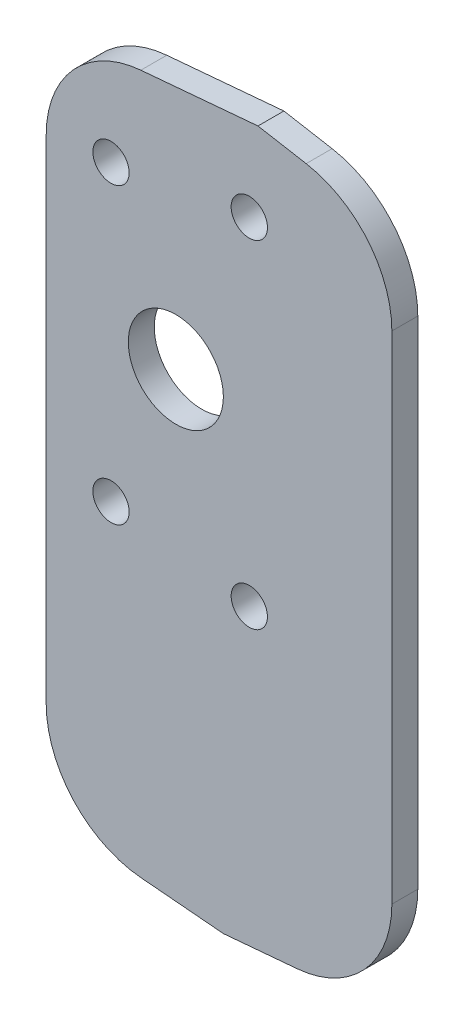
SolidWorks part; units mm, degrees
ref_plane "Face" through (0, 0, 0) normal (0, 0, 1) x (1, 0, 0)
ref_plane "Dessus" through (0, 0, 0) normal (0, 1, 0) x (1, 0, 0)
ref_plane "Droite" through (0, 0, 0) normal (1, 0, 0) x (0, 0, -1)
sketch "Esquisse2" plane through (0, 0, 0) normal (0, 0, 1) x (1, 0, 0)
  line L0 (-5.9599, 64.5276) -> (18.5449, 66.6715)
  line L1 (18.5449, 66.6715) -> (34.0401, 63.9392)
  line L2 (34.0401, 63.9392) -> (34.0401, -14.5608)
  line L3 (34.0401, -14.5608) -> (14.5449, -16.2664)
  line L4 (14.5449, -16.2664) -> (-5.9599, -14.4724)
  line L5 (-5.9599, -14.4724) -> (-5.9599, 64.5276)
  dimension "D1" = 95
  dimension "D2" = 100
  dimension "D3" = 95
  dimension "D4" = 95
  dimension "D5" = 40
  dimension "D6" = 4
  dimension "D7" = 79
  dimension "D8" = 78.5
extrude "Extrusion1" add sketch "Esquisse2" along normal blind 3
sketch "Esquisse3" plane through (0, 0, 3) normal (0, 0, 1) x (1, 0, 0)
  line L0 (-5.9599, 64.5276) -> (-5.9599, -14.4724) construction
  circle A0 centre (9.0401, 37.5276) radius 5.5
  dimension "D2" = 11
  dimension "D1" = 27
  dimension "D3" = 15
extrude "Enlèv. mat.-Extru.1" cut sketch "Esquisse3" against normal through all
fillet "Congé1" radius 12
sketch "Esquisse7" plane through (0, 0, 3) normal (0, 0, 1) x (1, 0, 0)
  circle A0 centre (9.0401, 37.5276) radius 5.5 construction
  point P0 (1.5401, 54.5276)
  point P1 (17.5401, 57.0276)
  point P2 (1.5401, 20.5276)
  point P3 (17.5401, 18.0276)
  dimension "D1" = 17
  dimension "D2" = 17
  dimension "D6" = 8.5
  dimension "D8" = 7.5
  dimension "D3" = 19.5
  dimension "D4" = 19.5
  dimension "D5" = 7.5
  dimension "D7" = 8.5
hole_wizard "Trou taraudé M5x0.82" positions "Esquisse3D3" profile "Esquisse8" tap size "M5x0.8" standard "ISO"
sketch3d "Esquisse3D3"
  point P0 (1.5401, 54.5276, 3)
  point P2 (17.5401, 57.0276, 3)
  point P4 (1.5401, 20.5276, 3)
  point P6 (17.5401, 18.0276, 3)
sketch "Esquisse8" plane through (1.5401, 54.5276, 3) normal (1, 0, 0) x (0, -1, 0)
  line L0 (0, 0) -> (0, 4.2618)
  line L1 (0, 4.2618) -> (2.1, 3)
  line L2 (2.1, 3) -> (2.1, 0)
  line L5 (2.1, 0) -> (0, 0)
  line L10 (0, 4.2618) -> (-2.1, 3) construction
  line L11 (0, -6.35) -> (0, 107.95) construction
  dimension "Diamètre du trou pour taraudage" = 4.2
  dimension "Profondeur du trou pour taraudage" = 3
  dimension "Angle de pointe" = 118
cosmetic thread "Représentation de filetage6" parameters "D1"=3, "D2"=5
cosmetic thread "Représentation de filetage7" parameters "D1"=3, "D2"=5
cosmetic thread "Représentation de filetage8" parameters "D1"=3, "D2"=5
cosmetic thread "Représentation de filetage9" parameters "D1"=3, "D2"=5
